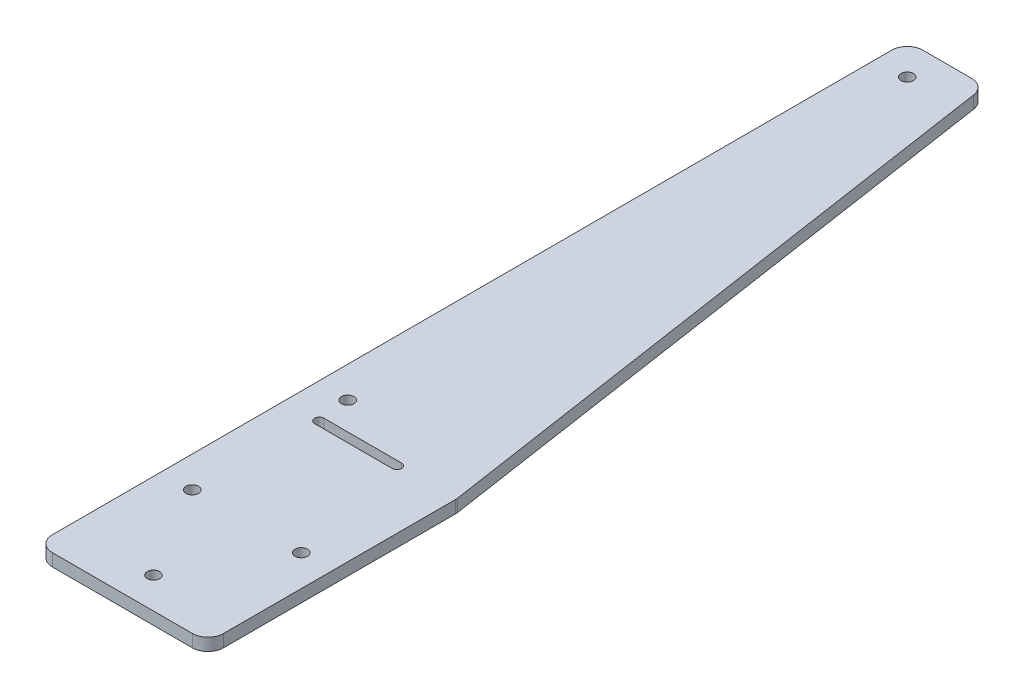
SolidWorks part; units mm, degrees
ref_plane "Front Plane" through (0, 0, 0) normal (0, 0, 1) x (1, 0, 0)
ref_plane "Top Plane" through (0, 0, 0) normal (0, 1, 0) x (1, 0, 0)
ref_plane "Right Plane" through (0, 0, 0) normal (1, 0, 0) x (0, 0, -1)
sketch "Sketch1" plane through (0, 0, 0) normal (0, 1, 0) x (1, 0, 0)
  line L0 (0, 64.5702) -> (0, -60.3774) construction
  line L1 (-50, -63.3962) -> (-50, 54.1038)
  line L2 (-47.5, 56.6038) -> (-39.6525, 56.6038)
  line L3 (-37.1803, 54.4751) -> (-22.5077, -43.2116)
  line L4 (-22.48, -43.5829) -> (-22.48, -63.3962)
  line L6 (-50, -63.3962) -> (-50, -78.3962)
  line L7 (-44.3882, -43.5829) -> (-31.8882, -43.5829) construction
  line L8 (-22.48, -78.3962) -> (-22.48, -63.3962)
  line L9 (-44.3882, -42.8329) -> (-31.8882, -42.8329)
  line L10 (-50, -78.3962) -> (-50, -80.8962)
  line L11 (-47.5, -83.3962) -> (-24.98, -83.3962)
  line L12 (-22.48, -80.8962) -> (-22.48, -78.3962)
  line L13 (-44.3882, -44.3329) -> (-31.8882, -44.3329)
  circle A0 centre (-36.24, -78.3962) radius 1
  circle A1 centre (-45, -63.3962) radius 1
  circle A2 centre (-27.48, -63.3962) radius 1
  circle A3 centre (-45, -38.3962) radius 1
  circle A4 centre (-45, 51.6038) radius 1
  arc A5 (-50, -80.8962) -> (-47.5, -83.3962) centre (-47.5, -80.8962) ccw
  arc A6 (-24.98, -83.3962) -> (-22.48, -80.8962) centre (-24.98, -80.8962) ccw
  arc A7 (-22.5077, -43.2116) -> (-22.48, -43.5829) centre (-24.98, -43.5829) cw
  arc A8 (-39.6525, 56.6038) -> (-37.1803, 54.4751) centre (-39.6525, 54.1038) cw
  arc A9 (-50, 54.1038) -> (-47.5, 56.6038) centre (-47.5, 54.1038) cw
  arc A10 (-44.3882, -42.8329) -> (-44.3882, -44.3329) centre (-44.3882, -43.5829) ccw
  arc A11 (-31.8882, -44.3329) -> (-31.8882, -42.8329) centre (-31.8882, -43.5829) ccw
  point P28 (-22.48, -43.3962)
  point P31 (-37.5, 56.6038)
  point P34 (-50, 56.6038)
  point P38 (-38.1382, -43.5829)
  dimension "D7" = 2
  dimension "D8" = 2.5
  dimension "D5" = 2
  dimension "D9" = 2
  dimension "D11" = 2.5
  dimension "D12" = 2.5
  dimension "D13" = 2.5
  dimension "D14" = 2.5
  dimension "D1" = 50
  dimension "D2" = 100
  dimension "D3" = 12.5
  dimension "D4" = 27.52
  dimension "D6" = 5
  dimension "D10" = 90
extrude "Boss-Extrude1" add sketch "Sketch1" along normal blind 2
